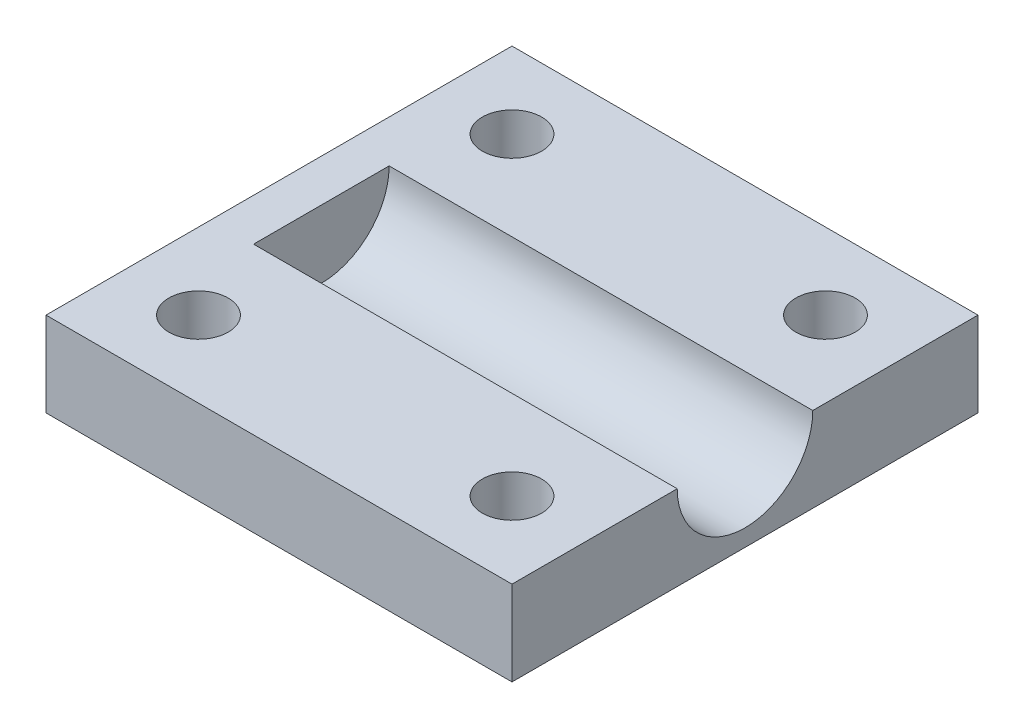
SolidWorks part; units mm, degrees
material "5052-H34"
ref_plane "Front Plane" through (0, 0, 0) normal (0, 0, 1) x (1, 0, 0)
ref_plane "Top Plane" through (0, 0, 0) normal (0, 1, 0) x (1, 0, 0)
ref_plane "Right Plane" through (0, 0, 0) normal (1, 0, 0) x (0, 0, -1)
sketch "Sketch1" plane through (0, 0, 0) normal (0, 1, 0) x (1, 0, 0)
  line L1 (-27.5, 27.5) -> (27.5, 27.5)
  line L2 (-27.5, 27.5) -> (-27.5, -27.5)
  line L3 (-27.5, -27.5) -> (27.5, -27.5)
  line L4 (27.5, 27.5) -> (27.5, -27.5)
  line L5 (-27.5, 27.5) -> (27.5, -27.5) construction
  line L6 (-27.5, -27.5) -> (27.5, 27.5) construction
  point P0 (0, 0)
  dimension "D1" = 55
  dimension "D2" = 55
extrude "Boss-Extrude1" add sketch "Sketch1" along normal blind 10
sketch "Sketch2" plane through (27.5, 0, 0) normal (1, 0, 0) x (0, 0, -1)
  line L0 (-27.5, 10) -> (27.5, 10) construction
  circle A0 centre (0, 10) radius 8
  dimension "D1" = 16
extrude "Cut-Extrude1" cut sketch "Sketch2" against normal blind 50
sketch "Sketch3" plane through (0, 10, 0) normal (0, 1, 0) x (1, 0, 0)
  line L0 (27.5, 27.5) -> (-27.5, 27.5) construction
  line L1 (-18.5, 18.5) -> (18.5, 18.5) construction
  line L2 (-18.5, 18.5) -> (-18.5, -18.5) construction
  line L3 (-18.5, -18.5) -> (18.5, -18.5) construction
  line L4 (18.5, 18.5) -> (18.5, -18.5) construction
  line L5 (-18.5, 18.5) -> (18.5, -18.5) construction
  line L6 (-18.5, -18.5) -> (18.5, 18.5) construction
  line L7 (27.5, 8) -> (27.5, 27.5) construction
  circle A0 centre (-18.5, 18.5) radius 3.5
  circle A1 centre (18.5, 18.5) radius 3.5
  circle A2 centre (-18.5, -18.5) radius 3.5
  circle A3 centre (18.5, -18.5) radius 3.5
  point P0 (0, 0)
  dimension "D3" = 7
  dimension "D1" = 9
  dimension "D2" = 9
extrude "Cut-Extrude2" cut sketch "Sketch3" against normal blind 5
cosmetic thread "Cosmetic Thread1" parameters "D2"=10
cosmetic thread "Cosmetic Thread2" parameters "D2"=10
cosmetic thread "Cosmetic Thread3" parameters "D2"=10
cosmetic thread "Cosmetic Thread4" parameters "D2"=10
